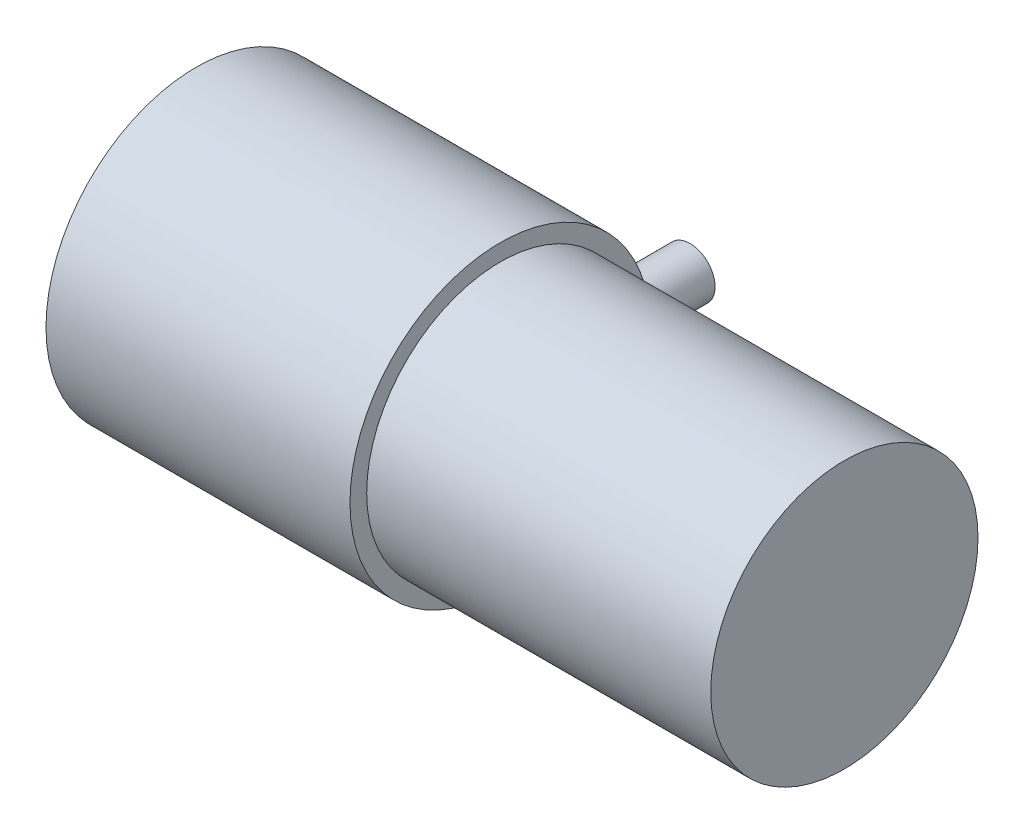
SolidWorks part; units mm, degrees
ref_plane "前视基准面" through (0, 0, 0) normal (0, 0, 1) x (1, 0, 0)
ref_plane "上视基准面" through (0, 0, 0) normal (0, 1, 0) x (1, 0, 0)
ref_plane "右视基准面" through (0, 0, 0) normal (1, 0, 0) x (0, 0, -1)
sketch "草图1" plane through (0, 0, 0) normal (1, 0, 0) x (0, 0, -1)
  circle A0 centre (0, 0) radius 13.5
  dimension "D1" = 27
extrude "凸台-拉伸1" add sketch "草图1" along normal blind 27.3
sketch "草图2" plane through (27.3, 0, 0) normal (1, 0, 0) x (0, 0, -1)
  circle A0 centre (0, 0) radius 12
  dimension "D1" = 24
extrude "凸台-拉伸2" add sketch "草图2" along normal blind 30.9
sketch "草图3" plane through (0, 0, 0) normal (-1, 0, 0) x (0, 0, 1)
  circle A0 centre (0, 0) radius 2.05
  dimension "D1" = 4.1
extrude "凸台-拉伸3" add sketch "草图3" along normal blind 6.2
ref_plane "基准面1" through (0, 0, -13.5) normal (0, 0, -1) x (-1, 0, 0)
sketch "草图4" plane through (0, 0, -13.5) normal (0, 0, -1) x (-1, 0, 0)
  circle A0 centre (-24.6389, 0) radius 2.25
  point P2 (-24.6389, 0)
  dimension "D1" = 4.5
extrude "凸台-拉伸4" add sketch "草图4" along normal blind 6.2 separate body
